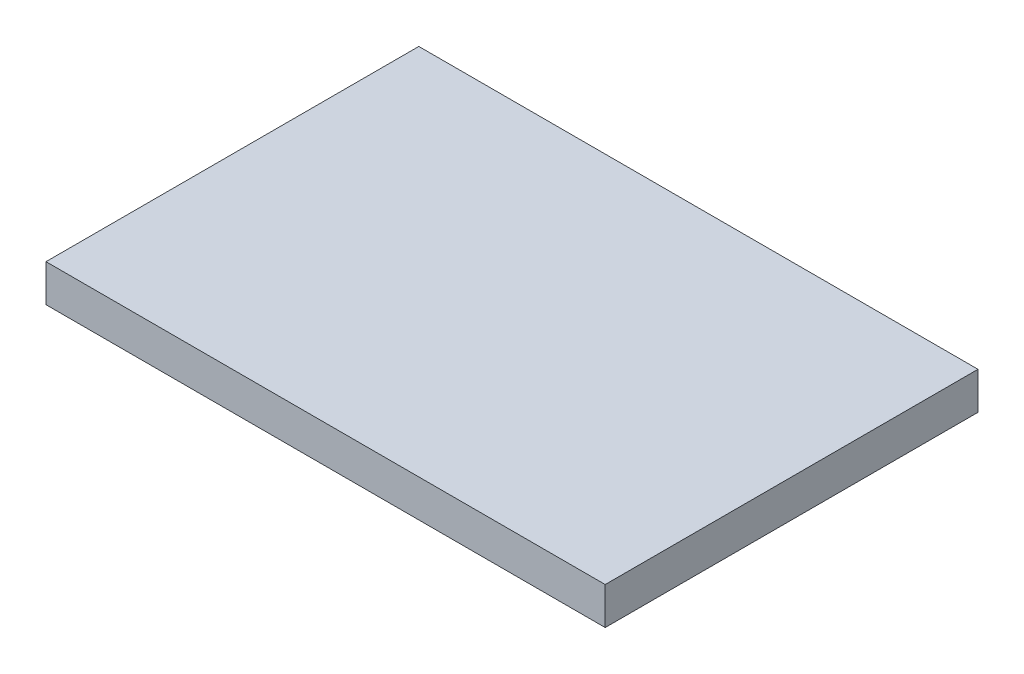
SolidWorks part; units mm, degrees
ref_plane "Front Plane" through (0, 0, 0) normal (0, 0, 1) x (1, 0, 0)
ref_plane "Top Plane" through (0, 0, 0) normal (0, 1, 0) x (1, 0, 0)
ref_plane "Right Plane" through (0, 0, 0) normal (1, 0, 0) x (0, 0, -1)
sketch "Sketch1" plane through (0, 0, 0) normal (0, 1, 0) x (1, 0, 0)
  line L1 (-61.845, 19.9262) -> (-1.845, 19.9262)
  line L2 (-61.845, 19.9262) -> (-61.845, -20.0738)
  line L3 (-61.845, -20.0738) -> (-1.845, -20.0738)
  line L4 (-1.845, 19.9262) -> (-1.845, -20.0738)
  line L5 (-31.845, -20.0738) -> (-31.845, 19.9262) construction
  line L6 (-61.845, -0.0738) -> (-1.845, -0.0738) construction
  point P0 (-31.845, -0.0738)
  dimension "D1" = 60
  dimension "D2" = 40
extrude "Boss-Extrude1" add sketch "Sketch1" along normal blind 4
